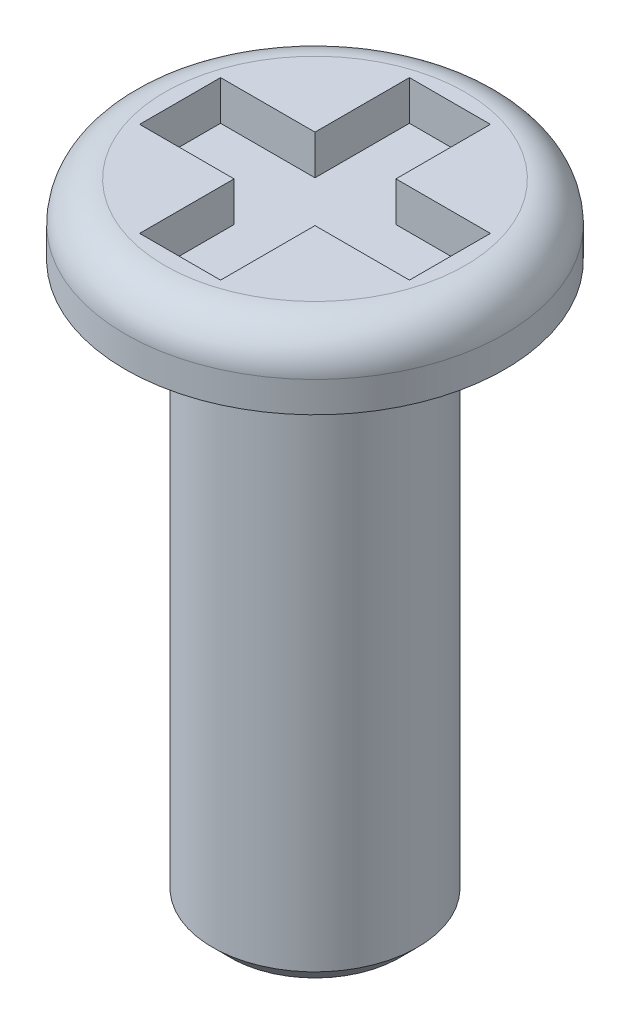
SolidWorks part; units mm, degrees
material "Plain Carbon Steel"
ref_plane "Front Plane" through (0, 0, 0) normal (0, 0, 1) x (1, 0, 0)
ref_plane "Top Plane" through (0, 0, 0) normal (0, 1, 0) x (1, 0, 0)
ref_plane "Right Plane" through (0, 0, 0) normal (1, 0, 0) x (0, 0, -1)
sketch "Sketch1" plane through (0, 0, 0) normal (0, 0, 1) x (1, 0, 0)
  line L0 (2.6797, 0.9906) -> (0, 0.9906)
  line L1 (0, 0.9906) -> (0, 0)
  line L2 (0, 0) -> (2.6797, 0)
  line L3 (2.6797, 0) -> (2.6797, 0.9906)
  line L4 (0, 0.9906) -> (0, 0) construction
revolve "Revolve1" add sketch "Sketch1" angle 360 about L4
sketch "Sketch2" plane through (0, 0, 0) normal (0, -1, 0) x (1, 0, 0)
  circle A0 centre (0, 0) radius 1.4478
extrude "Boss-Extrude1" add sketch "Sketch2" along normal blind 7.9375
sketch "Sketch3" plane through (0, 0.9906, 0) normal (0, 1, 0) x (-1, 0, 0)
  line L0 (-0.5715, -0.5715) -> (-0.5715, -1.905)
  line L1 (-0.5715, -1.905) -> (0.5715, -1.905)
  line L2 (0.5715, -1.905) -> (0.5715, -0.5715)
  line L3 (0.5715, -0.5715) -> (1.905, -0.5715)
  line L4 (1.905, -0.5715) -> (1.905, 0.5715)
  line L5 (1.905, 0.5715) -> (0.5715, 0.5715)
  line L6 (0.5715, 0.5715) -> (0.5715, 1.905)
  line L7 (0.5715, 1.905) -> (-0.5715, 1.905)
  line L8 (-0.5715, 1.905) -> (-0.5715, 0.5715)
  line L9 (-0.5715, 0.5715) -> (-1.905, 0.5715)
  line L10 (-1.905, 0.5715) -> (-1.905, -0.5715)
  line L11 (-1.905, -0.5715) -> (-0.5715, -0.5715)
extrude "Cut-Extrude1" cut sketch "Sketch3" against normal blind 0.5588
chamfer "Chamfer1" distance 0.254 angle 45 1 edges at (0, -7.9375, -1.4478)
fillet "Fillet1" radius 0.254 1 edges at (0, 0, -1.4478)
fillet "Fillet2" radius 0.5588 1 edges at (0, 0.9906, -2.6797)
